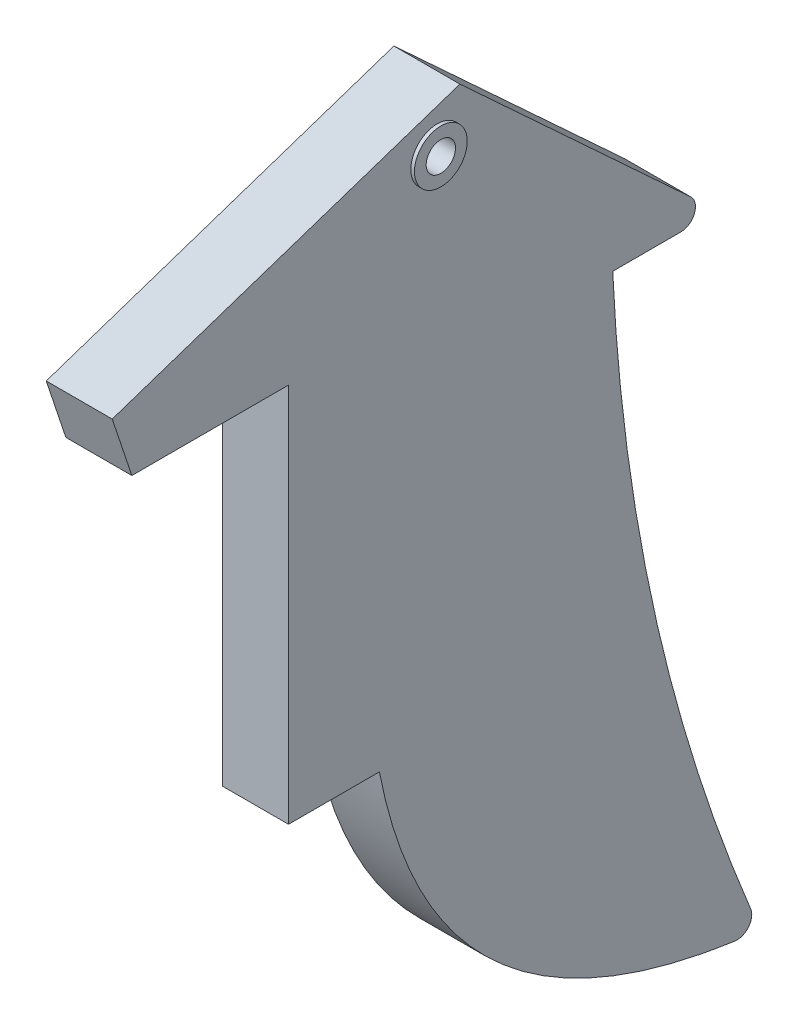
SolidWorks part; units mm, degrees
ref_plane "Front Plane" through (0, 0, 0) normal (0, 0, 1) x (1, 0, 0)
ref_plane "Top Plane" through (0, 0, 0) normal (0, 1, 0) x (1, 0, 0)
ref_plane "Right Plane" through (0, 0, 0) normal (1, 0, 0) x (0, 0, -1)
sketch "Sketch3" plane through (0, 0, 0) normal (1, 0, 0) x (0, 0, -1)
  line L0 (0, 0) -> (-23.7098, -7.9274)
  line L2 (-22.3708, -11.9324) -> (-11.6858, -11.9324)
  line L3 (-11.6858, -11.9324) -> (-11.6858, -37.874)
  line L4 (-11.6858, -37.874) -> (-5.4886, -37.874)
  line L5 (10.4232, -16.2676) -> (17.6253, -16.2676)
  line L6 (17.6253, -16.2676) -> (0, 0)
  line L7 (-23.7098, -7.9274) -> (-22.3708, -11.9324)
  spline S0 degree 2 poles (-5.4886, -37.874) (-1.6432, -57.8903) (20.4966, -60.1993) knots 0 0 0 1 1 1
  spline S1 degree 2 poles (20.4966, -60.1993) (11.481, -39.197) (10.4232, -16.2676) knots 0 0 0 1 1 1
  dimension "D1" = 25
extrude "Boss-Extrude2" add sketch "Sketch3" along normal blind 4.5
sketch "Sketch4" plane through (4.5, 0, 0) normal (1, 0, 0) x (0, 0, -1)
  circle A0 centre (-1.5493, -3.3722) radius 1
extrude "Cut-Extrude2" cut sketch "Sketch4" against normal through all both and the other way through all
fillet "Fillet1" radius 1 1 edges at (2.25, -16.2676, -17.6253)
fillet "Fillet2" radius 1 1 edges at (2.25, -60.1993, -20.4966)
sketch "Sketch5" plane through (4.5, 0, 0) normal (1, 0, 0) x (0, 0, -1)
  circle A0 centre (-1.5493, -3.3722) radius 1.8
extrude "Boss-Extrude3" add sketch "Sketch5" along normal blind 0.25
sketch "Sketch7" plane through (4.75, 0, 0) normal (1, 0, 0) x (0, 0, -1)
  circle A0 centre (-1.5493, -3.3722) radius 1
  circle A1 centre (-1.5493, -3.3722) radius 1.8 construction
  dimension "D1" = 0
extrude "Cut-Extrude3" cut sketch "Sketch7" against normal through all
ref_plane "Plane1" through (2.25, 0, 0) normal (1, 0, 0) x (0, 0, -1)
mirror "Mirror1" about plane through (2.25, 0, 0) normal (1, 0, 0) of "Boss-Extrude3", "Cut-Extrude3"
